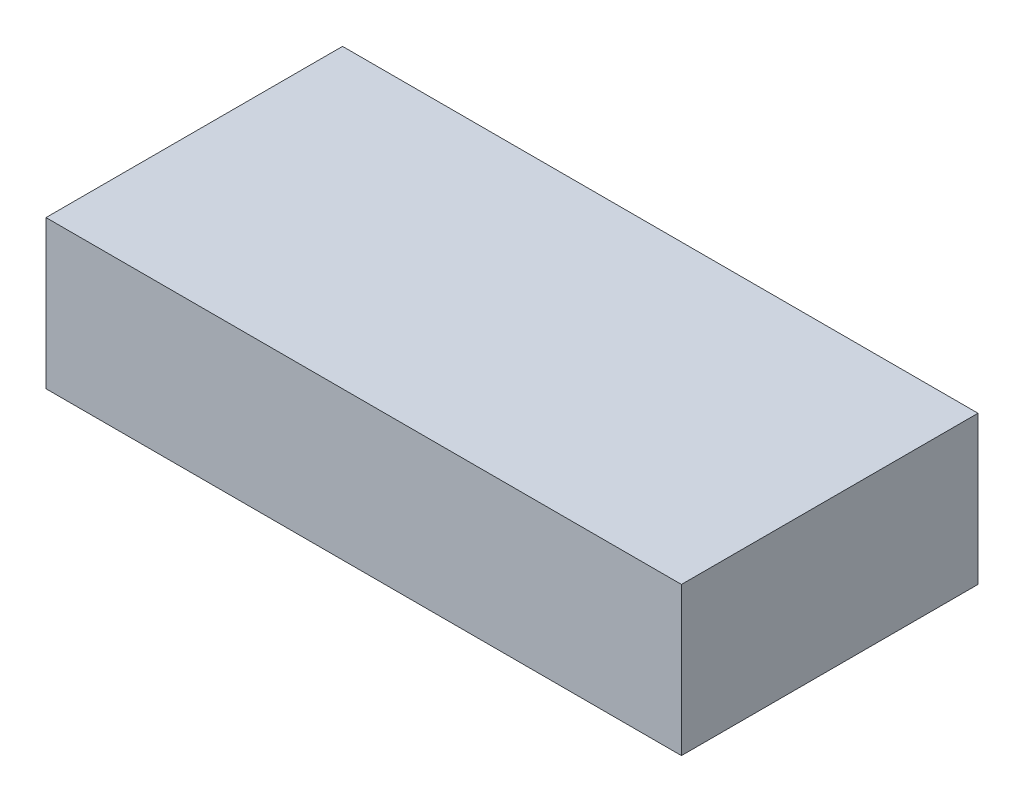
SolidWorks part; units mm, degrees
ref_plane "Front Plane" through (0, 0, 0) normal (0, 0, 1) x (1, 0, 0)
ref_plane "Top Plane" through (0, 0, 0) normal (0, 1, 0) x (1, 0, 0)
ref_plane "Right Plane" through (0, 0, 0) normal (1, 0, 0) x (0, 0, -1)
sketch "Sketch1" plane through (0, 0, 0) normal (0, 1, 0) x (1, 0, 0)
  line L1 (-15, -7) -> (15, -7)
  line L2 (-15, -7) -> (-15, 7)
  line L3 (-15, 7) -> (15, 7)
  line L4 (15, -7) -> (15, 7)
  line L5 (-15, -7) -> (15, 7) construction
  line L6 (-15, 7) -> (15, -7) construction
  point P0 (0, 0)
  dimension "D1" = 14
  dimension "D2" = 30
extrude "Boss-Extrude1" add sketch "Sketch1" along normal blind 7
